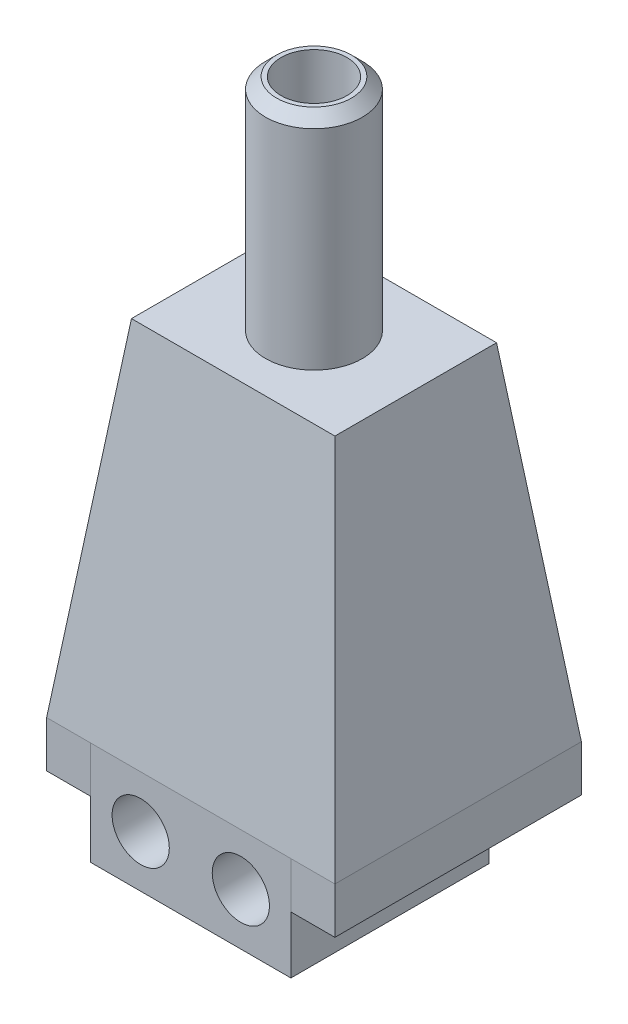
SolidWorks part; units mm, degrees
ref_plane "Plano frontal" through (0, 0, 0) normal (0, 0, 1) x (1, 0, 0)
ref_plane "Plano superior" through (0, 0, 0) normal (0, 1, 0) x (1, 0, 0)
ref_plane "Plano direito" through (0, 0, 0) normal (1, 0, 0) x (0, 0, -1)
sketch "Esboço1" plane through (0, 0, 0) normal (0, 1, 0) x (1, 0, 0)
  line L1 (-4.55, -4.5) -> (4.55, -4.5)
  line L2 (-4.55, -4.5) -> (-4.55, 4.5)
  line L3 (-4.55, 4.5) -> (4.55, 4.5)
  line L4 (4.55, -4.5) -> (4.55, 4.5)
  line L5 (-4.55, -4.5) -> (4.55, 4.5) construction
  line L6 (-4.55, 4.5) -> (4.55, -4.5) construction
  point P0 (0, 0)
  dimension "D1" = 9
  dimension "D2" = 9.1
extrude "Ressalto-extrusão1" add sketch "Esboço1" along normal blind 4.7
sketch "Esboço2" plane through (0, 4.7, 0) normal (0, 1, 0) x (1, 0, 0)
  line L0 (-4.55, -4.5) -> (4.55, -4.5) construction
  line L1 (-6.55, -4.5) -> (6.55, -4.5)
  line L2 (-6.55, -4.5) -> (-6.55, 6.7)
  line L3 (-6.55, 6.7) -> (6.55, 6.7)
  line L4 (6.55, -4.5) -> (6.55, 6.7)
  line L5 (0, 6.7) -> (0, 0) construction
  dimension "D1" = 13.1
  dimension "D2" = 11.2
extrude "Ressalto-extrusão2" add sketch "Esboço2" along normal blind 15.7 draft 7 separate body
sketch "Esboço3" plane through (0, 20.4, 0) normal (0, 1, 0) x (1, 0, 0)
  line L0 (4.6223, -2.5723) -> (-4.6223, 4.7723) construction
  circle A0 centre (0, 1.1) radius 2.2
  point P6 (0, 0)
  dimension "D1" = 4.4
extrude "Ressalto-extrusão3" add sketch "Esboço3" along normal blind 10
shell "Casca1" thickness 0.7
chamfer "Chanfro1" distance 0.5 angle 45 1 edges at (0, 30.4, 1.1)
sketch "Esboço4" plane through (0, 0, 4.5) normal (0, 0, 1) x (1, 0, 0)
  line L0 (0, 0) -> (0, 4.7) construction
  line L1 (-4.55, 0) -> (4.55, 0) construction
  line L2 (-6.55, 4.7) -> (6.55, 4.7) construction
  line L3 (0, 0) -> (-4.55, 4.7) construction
  circle A0 centre (-2.275, 2.35) radius 1.3
  circle A2 centre (2.275, 2.35) radius 1.3
  point P4 (0, 0)
  point P13 (0, 0)
  dimension "D1" = 2.6
extrude "Corte-extrusão1" cut sketch "Esboço4" against normal blind 2
sketch "Esboço5" plane through (0, 4.7, 0) normal (0, -1, 0) x (1, 0, 0)
  line L4 (-6.55, 4.5) -> (-6.55, -6.7)
  line L5 (-6.55, -6.7) -> (6.55, -6.7)
  line L6 (6.55, -6.7) -> (6.55, 4.5)
  line L7 (6.55, 4.5) -> (-6.55, 4.5)
  line L8 (-6.55, 4.5) -> (-6.55, -6.7)
  line L9 (-6.55, -6.7) -> (6.55, -6.7)
  line L10 (6.55, -6.7) -> (6.55, 4.5)
  line L11 (6.55, 4.5) -> (-6.55, 4.5)
  line L12 (4.55, -4.5) -> (4.55, 4.5)
  line L13 (4.55, 4.5) -> (-4.55, 4.5)
  line L14 (-4.55, 4.5) -> (-4.55, -4.5)
  line L15 (-4.55, -4.5) -> (4.55, -4.5)
  line L16 (4.55, -4.5) -> (4.55, 4.5)
  line L17 (4.55, 4.5) -> (-4.55, 4.5)
  line L18 (-4.55, 4.5) -> (-4.55, -4.5)
  line L19 (-4.55, -4.5) -> (4.55, -4.5)
  line M9 (-6.55, 4.5) -> (-6.55, -6.7)
  line M10 (-6.55, -6.7) -> (6.55, -6.7)
  line M11 (6.55, -6.7) -> (6.55, 4.5)
  line M12 (6.55, 4.5) -> (-6.55, 4.5)
  dimension "D1" = 0
  dimension "D2" = 0
extrude "Ressalto-extrusão4" add sketch "Esboço5" along normal blind 2.1 separate body contours L19 L18 L16 M12 M9 M10 M11
